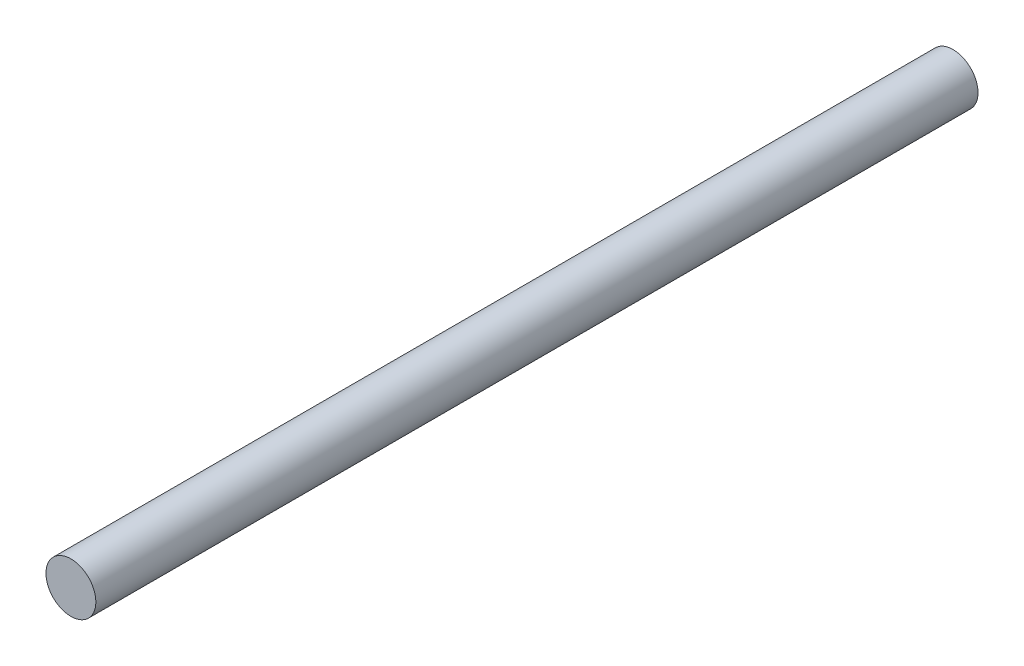
SolidWorks part; units mm, degrees
ref_plane "Front Plane" through (0, 0, 0) normal (0, 0, 1) x (1, 0, 0)
ref_plane "Top Plane" through (0, 0, 0) normal (0, 1, 0) x (1, 0, 0)
ref_plane "Right Plane" through (0, 0, 0) normal (1, 0, 0) x (0, 0, -1)
sketch "Sketch1" plane through (0, 0, 0) normal (0, 0, 1) x (1, 0, 0)
  circle A0 centre (0, 0) radius 12.5
  dimension "D1" = 25
extrude "Boss-Extrude1" add sketch "Sketch1" along normal mid plane 442
